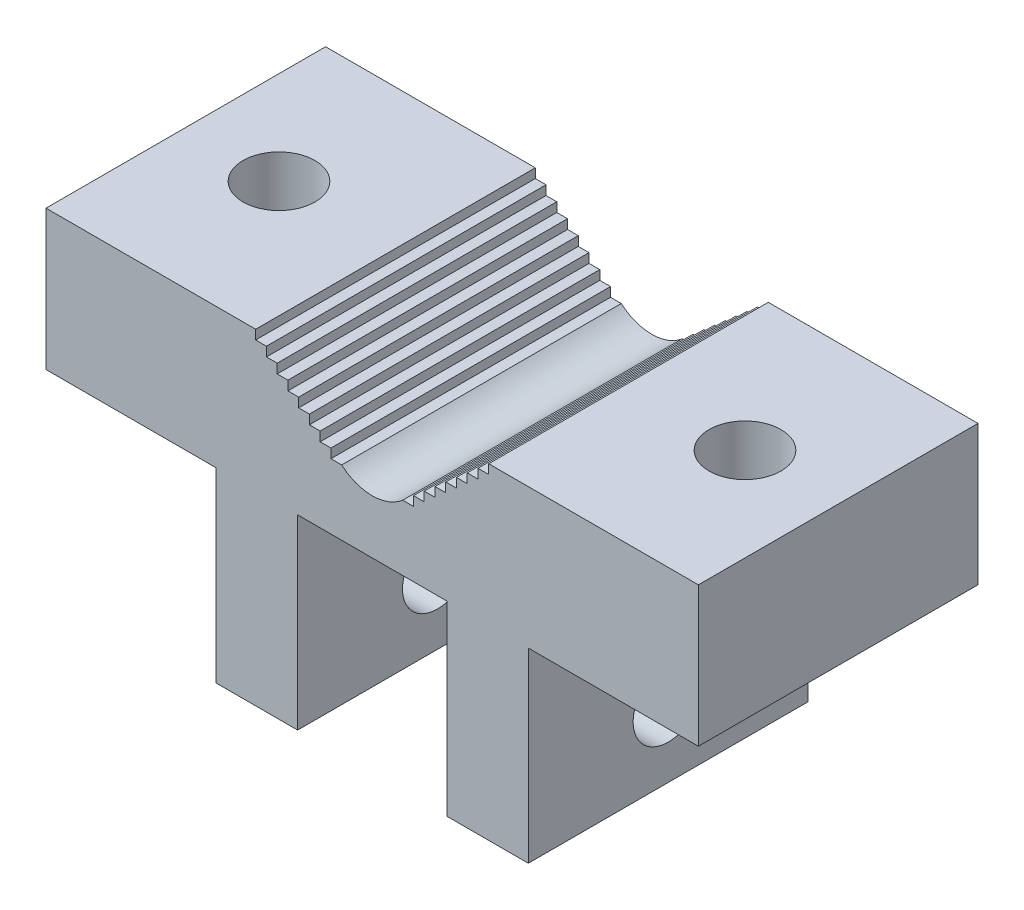
SolidWorks part; units mm, degrees
material "6061-T6 (SS)"
ref_plane "Front Plane" through (0, 0, 0) normal (0, 0, 1) x (1, 0, 0)
ref_plane "Top Plane" through (0, 0, 0) normal (0, 1, 0) x (1, 0, 0)
ref_plane "Right Plane" through (0, 0, 0) normal (1, 0, 0) x (0, 0, -1)
sketch "Sketch1" plane through (0, 0, 0) normal (0, 0, 1) x (1, 0, 0)
  line L0 (-44.45, 0) -> (44.45, 0)
  line L1 (44.45, 0) -> (44.45, 19.05)
  line L2 (44.45, 19.05) -> (-44.45, 19.05)
  line L3 (-44.45, 19.05) -> (-44.45, 0)
  point P3 (0, 0)
  dimension "D1" = 19.05
  dimension "D2" = 88.9
extrude "Boss-Extrude1" add sketch "Sketch1" against normal blind 38.1
sketch "Sketch2" plane through (0, 0, 0) normal (0, 0, 1) x (1, 0, 0)
  line L0 (-15.875, 19.05) -> (-4.1606, 8.89) construction
  line L1 (-15.875, 19.05) -> (0, 19.05)
  line L2 (44.45, 19.05) -> (-44.45, 19.05) construction
  line L3 (15.875, 19.05) -> (4.1606, 8.89) construction
  line L4 (15.875, 19.05) -> (0, 19.05)
  line L5 (-15.875, 19.05) -> (-15.875, 17.78)
  line L6 (-15.875, 17.78) -> (-14.4107, 17.78)
  line L7 (-14.4107, 17.78) -> (-14.4107, 16.51)
  line L8 (-14.4107, 16.51) -> (-12.9464, 16.51)
  line L9 (-12.9464, 16.51) -> (-12.9464, 15.24)
  line L10 (-12.9464, 15.24) -> (-11.4821, 15.24)
  line L11 (-11.4821, 15.24) -> (-11.4821, 13.97)
  line L12 (-11.4821, 13.97) -> (-10.0178, 13.97)
  line L13 (-10.0178, 13.97) -> (-10.0178, 12.7)
  line L14 (-10.0178, 12.7) -> (-8.5535, 12.7)
  line L15 (-8.5535, 12.7) -> (-8.5535, 11.43)
  line L16 (-8.5535, 11.43) -> (-7.0892, 11.43)
  line L17 (-7.0892, 11.43) -> (-7.0892, 10.16)
  line L18 (-7.0892, 10.16) -> (-5.6249, 10.16)
  line L19 (-5.6249, 10.16) -> (-5.6249, 8.89)
  line L20 (-5.6249, 8.89) -> (-4.1606, 8.89)
  line L21 (0, 19.05) -> (0, 0) construction
  line L24 (5.6249, 8.89) -> (4.1606, 8.89)
  line L25 (5.6249, 10.16) -> (5.6249, 8.89)
  line L26 (7.0892, 10.16) -> (5.6249, 10.16)
  line L27 (7.0892, 11.43) -> (7.0892, 10.16)
  line L28 (8.5535, 11.43) -> (7.0892, 11.43)
  line L29 (8.5535, 12.7) -> (8.5535, 11.43)
  line L30 (10.0178, 12.7) -> (8.5535, 12.7)
  line L31 (10.0178, 13.97) -> (10.0178, 12.7)
  line L32 (11.4821, 13.97) -> (10.0178, 13.97)
  line L33 (11.4821, 15.24) -> (11.4821, 13.97)
  line L34 (12.9464, 15.24) -> (11.4821, 15.24)
  line L35 (12.9464, 16.51) -> (12.9464, 15.24)
  line L36 (14.4107, 16.51) -> (12.9464, 16.51)
  line L37 (14.4107, 17.78) -> (14.4107, 16.51)
  line L38 (15.875, 17.78) -> (14.4107, 17.78)
  line L39 (15.875, 19.05) -> (15.875, 17.78)
  arc A0 (4.1606, 8.89) -> (-4.1606, 8.89) centre (0, 13.6871) cw
  point P7 (0, 19.05)
  dimension "D1" = 6.35
  dimension "D2" = 31.75
  dimension "D4" = 1.27
extrude "Cut-Extrude1" cut sketch "Sketch2" against normal up to next
sketch "Sketch3" plane through (0, 0, 0) normal (0, 0, 1) x (1, 0, 0)
  circle A0 centre (0, 24.151) radius 14.2875
  dimension "D1" = 28.575
hole_wizard "3/8 Clearance Hole1" positions "Sketch6" profile "Sketch5" hole size "3/8" standard "ANSI Inch" end condition through all
sketch "Sketch6" plane through (0, 19.05, 0) normal (0, 1, 0) x (1, 0, 0)
  line L1 (-44.45, 38.1) -> (-44.45, 0) construction
  line L3 (44.45, 38.1) -> (44.45, 0) construction
  point P0 (-31.75, 19.05)
  point P2 (31.75, 19.05)
  point P10 (-44.45, 19.05)
  point P16 (44.45, 19.05)
  dimension "D1" = 12.7
  dimension "D2" = 12.7
sketch "Sketch5" plane through (-31.75, 19.05, -19.05) normal (1, 0, 0) x (0, 0, 1)
  line L0 (0, 0) -> (0, 19.05)
  line L1 (0, 19.05) -> (4.9022, 19.05)
  line L2 (4.9022, 19.05) -> (4.9022, 0)
  line L5 (4.9022, 0) -> (0, 0)
  line L11 (0, -6.35) -> (0, 107.95) construction
  dimension "Thru Hole Dia." = 9.8044
  dimension "Thru Hole Depth" = 19.05
sketch "Sketch7" plane through (0, 0, 0) normal (0, -1, 0) x (1, 0, 0)
  line L0 (-10.16, 0) -> (-10.16, -38.1)
  line L1 (-44.45, 0) -> (44.45, 0) construction
  line L2 (-44.45, -38.1) -> (44.45, -38.1) construction
  line L3 (-10.16, -38.1) -> (-21.2725, -38.1)
  line L4 (-21.2725, -38.1) -> (-21.2725, 0)
  line L5 (-21.2725, 0) -> (-10.16, 0)
  line L6 (0, 0) -> (0, -38.1) construction
  line L7 (10.16, -38.1) -> (21.2725, -38.1)
  line L8 (21.2725, -38.1) -> (21.2725, 0)
  line L9 (21.2725, 0) -> (10.16, 0)
  line L10 (10.16, 0) -> (10.16, -38.1)
  dimension "D1" = 11.1125
  dimension "D2" = 10.16
extrude "Boss-Extrude2" add sketch "Sketch7" along normal blind 25.4
hole_wizard "3/8 (0.375) Diameter Hole1" positions "Sketch8" profile "Sketch9" hole size "3/8" standard "ANSI Inch" end condition through all
sketch "Sketch8" plane through (21.2725, 0, 0) normal (1, 0, 0) x (0, 0, -1)
  line L1 (38.1, -25.4) -> (0, -25.4) construction
  line L2 (38.1, 0) -> (0, 0) construction
  point P0 (19.05, -15.875)
  point P10 (19.05, -25.4)
  dimension "D1" = 15.875
sketch "Sketch9" plane through (21.2725, -15.875, -19.05) normal (0, 1, 0) x (0, 0, -1)
  line L0 (0, 0) -> (0, 65.7225)
  line L1 (0, 65.7225) -> (4.7625, 65.7225)
  line L2 (4.7625, 65.7225) -> (4.7625, 0)
  line L5 (4.7625, 0) -> (0, 0)
  line L11 (0, -6.35) -> (0, 107.95) construction
  dimension "Thru Hole Dia." = 9.525
  dimension "Thru Hole Depth" = 65.7225
